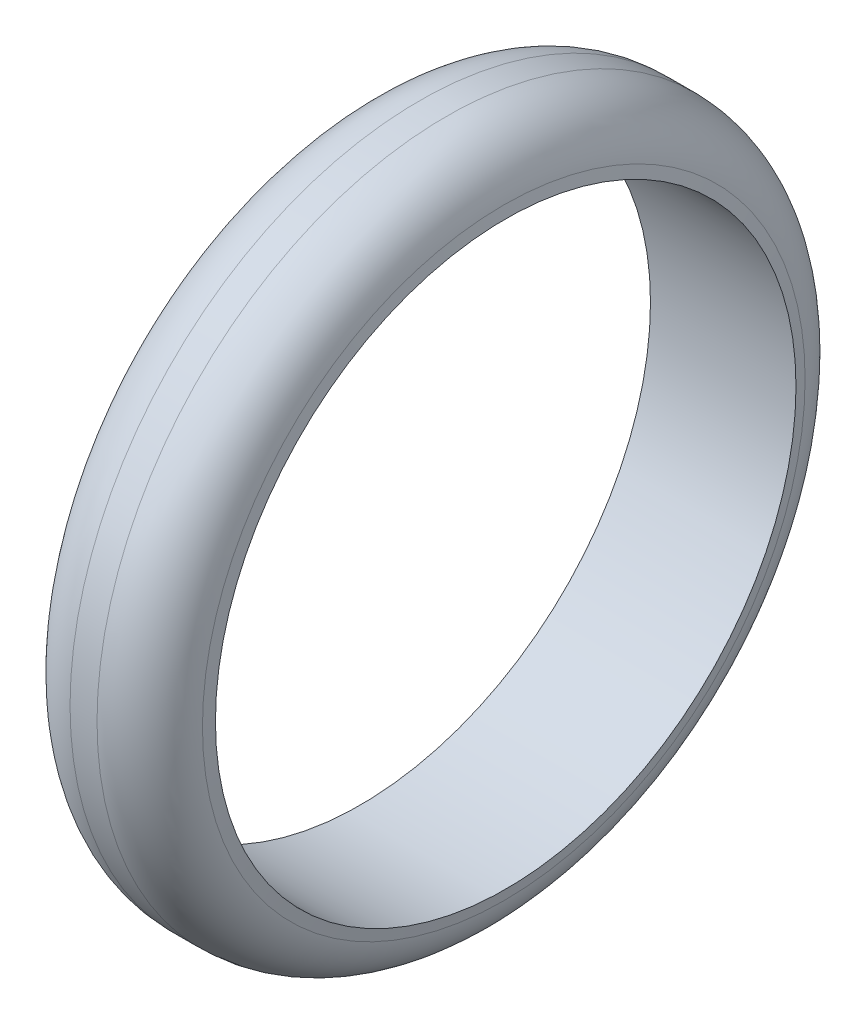
SolidWorks part; units mm, degrees
ref_plane "Front Plane" through (0, 0, 0) normal (0, 0, 1) x (1, 0, 0)
ref_plane "Top Plane" through (0, 0, 0) normal (0, 1, 0) x (1, 0, 0)
ref_plane "Right Plane" through (0, 0, 0) normal (1, 0, 0) x (0, 0, -1)
sketch "Sketch1" plane through (0, 0, 0) normal (0, 0, 1) x (1, 0, 0)
  line L0 (0, 0) -> (0, 51.9092) construction
  line L1 (0, 0) -> (71.5432, 0) construction
  line L2 (-8.5667, 48.0246) -> (8.5667, 48.0246)
  line L3 (8.5667, 48.0246) -> (10, 39.8957)
  line L4 (10, 39.8957) -> (-10, 39.8957)
  line L6 (0, 48.0246) -> (85.1531, 48.0246)
  line L7 (85.1531, 48.0246) -> (85.1531, -61.9754)
  line L8 (85.1531, -61.9754) -> (-8.5667, -61.9754)
  line L9 (10, 39.8957) -> (73.5121, 39.8957)
  line L10 (73.5121, 39.8957) -> (73.5121, -40.1043)
  line L11 (73.5121, -40.1043) -> (1.8086, -38.49)
  line L12 (26.0044, -39.0347) -> (1.8086, -38.49)
  line L13 (-8.5667, 48.0246) -> (-10, 39.8957)
  point P21 (0, 39.8957)
  dimension "D1" = 80
  dimension "D2" = 110
  dimension "D3" = 20
  dimension "D4" = 10
revolve "Revolve8" add sketch "Sketch1" angle 360 about L1
fillet "Fillet1" radius 8 1 edges at (-8.5667, 0, 48.0246)
fillet "Fillet2" radius 8 1 edges at (8.5667, 0, 48.0246)
